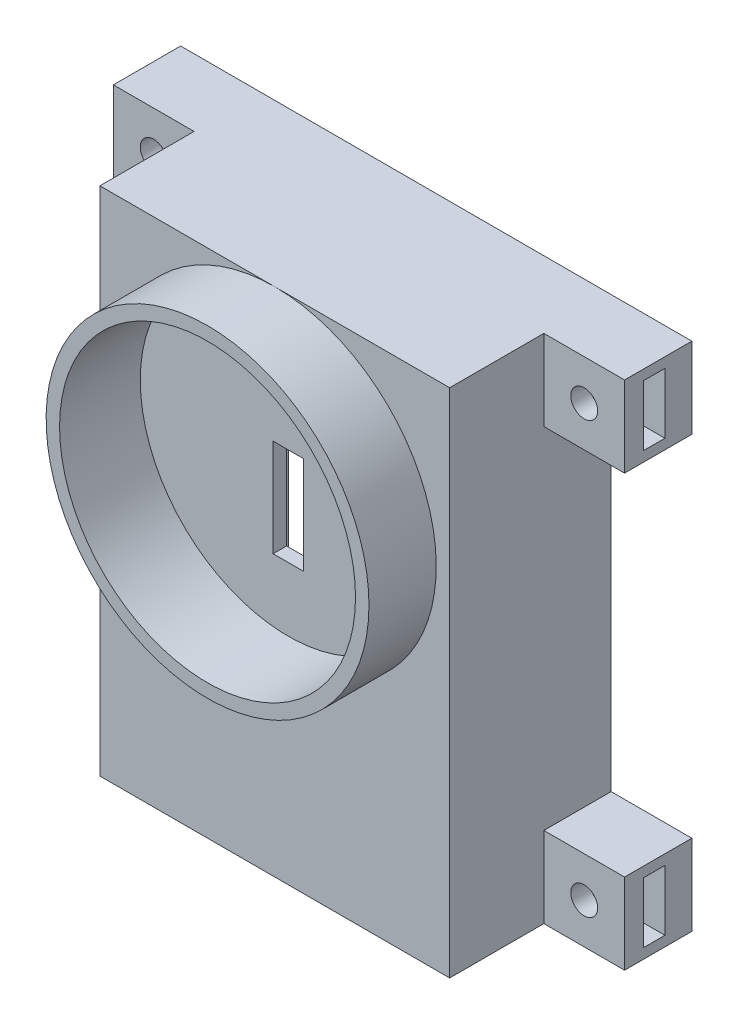
SolidWorks part; units mm, degrees
ref_plane "正面" through (0, 0, 0) normal (0, 0, 1) x (1, 0, 0)
ref_plane "平面" through (0, 0, 0) normal (0, 1, 0) x (1, 0, 0)
ref_plane "右側面" through (0, 0, 0) normal (1, 0, 0) x (0, 0, -1)
sketch "ｽｹｯﾁ1" plane through (0, 0, 0) normal (0, 0, 1) x (1, 0, 0)
  line L1 (13, -19) -> (-13, -19)
  line L2 (13, -19) -> (13, 19)
  line L3 (13, 19) -> (-13, 19)
  line L4 (-13, -19) -> (-13, 19)
  line L5 (13, -19) -> (-13, 19) construction
  line L6 (13, 19) -> (-13, -19) construction
  point P0 (0, 0)
  dimension "D1" = 38
  dimension "D2" = 26
extrude "ﾎﾞｽ - 押し出し1" add sketch "ｽｹｯﾁ1" along normal blind 12
sketch "ｽｹｯﾁ2" plane through (0, 0, 0) normal (0, 0, 1) x (1, 0, 0)
  line L1 (11, -17) -> (-11, -17)
  line L2 (11, -17) -> (11, 17)
  line L3 (11, 17) -> (-11, 17)
  line L4 (-11, -17) -> (-11, 17)
  line L5 (11, -17) -> (-11, 17) construction
  line L6 (11, 17) -> (-11, -17) construction
  point P0 (0, 0)
  dimension "D1" = 22
  dimension "D2" = 34
extrude "ｶｯﾄ - 押し出し1" cut sketch "ｽｹｯﾁ2" along normal blind 10
sketch "ｽｹｯﾁ3" plane through (0, 0, 0) normal (0, 0, 1) x (1, 0, 0)
  line L0 (13, 19) -> (-13, 19) construction
  line L1 (-1.125, 0.75) -> (1.125, 0.75)
  line L2 (-1.125, 0.75) -> (-1.125, 8)
  line L3 (-1.125, 8) -> (1.125, 8)
  line L4 (1.125, 0.75) -> (1.125, 8)
  line L5 (-1.125, 0.75) -> (1.125, 8) construction
  line L6 (-1.125, 8) -> (1.125, 0.75) construction
  point P0 (0, 4.375)
  dimension "D1" = 7.25
  dimension "D2" = 2.25
  dimension "D3" = 11
extrude "ｶｯﾄ - 押し出し3" cut sketch "ｽｹｯﾁ3" along normal blind 12
sketch "ｽｹｯﾁ4" plane through (0, 0, 0) normal (0, 0, 1) x (1, 0, 0)
  line L0 (13, -19) -> (13, 19) construction
  line L1 (13, 19) -> (19, 19)
  line L2 (13, 19) -> (13, 13)
  line L3 (13, 13) -> (19, 13)
  line L4 (19, 19) -> (19, 13)
  line L5 (13, -19) -> (19, -19)
  line L6 (13, -19) -> (13, -13)
  line L7 (13, -13) -> (19, -13)
  line L8 (19, -19) -> (19, -13)
  line L9 (-13, -19) -> (13, -19) construction
  line L10 (-13, -19) -> (-19, -19)
  line L11 (-13, -19) -> (-13, -13)
  line L12 (-13, -13) -> (-19, -13)
  line L13 (-19, -19) -> (-19, -13)
  line L14 (-13, 19) -> (-19, 19)
  line L15 (-13, 19) -> (-13, 13)
  line L16 (-13, 13) -> (-19, 13)
  line L17 (-19, 19) -> (-19, 13)
  dimension "D1" = 6
  dimension "D2" = 6
  dimension "D3" = 6
  dimension "D4" = 6
  dimension "D5" = 6
  dimension "D6" = 6
  dimension "D7" = 6
  dimension "D8" = 6
  dimension "D9" = 6
extrude "ﾎﾞｽ - 押し出し2" add sketch "ｽｹｯﾁ4" along normal blind 5
sketch "ｽｹｯﾁ5" plane through (0, 0, 0) normal (0, 0, 1) x (1, 0, 0)
  line L0 (-13, 19) -> (-19, 19) construction
  line L1 (-19, 19) -> (-19, 13) construction
  line L2 (-13, -13) -> (-19, -13) construction
  line L3 (19, -19) -> (19, -13) construction
  line L5 (13, 13) -> (19, 13) construction
  line L7 (19, -13) -> (13, -13) construction
  circle A0 centre (-16, 16) radius 1
  circle A1 centre (-16, -16) radius 1
  circle A2 centre (16, -16) radius 1
  circle A3 centre (16, 16) radius 1
  point P16 (16, 13)
  dimension "D1" = 3
  dimension "D2" = 3
  dimension "D3" = 3
  dimension "D4" = 2
  dimension "D5" = 2
  dimension "D6" = 3
  dimension "D7" = 2
  dimension "D8" = 2
  dimension "D9" = 3
  dimension "D10" = 3
extrude "ｶｯﾄ - 押し出し4" cut sketch "ｽｹｯﾁ5" along normal through all
sketch "ｽｹｯﾁ6" plane through (0, 0, 0) normal (0, 0, 1) x (1, 0, 0)
  line L0 (-19, 19) -> (-19, 13) construction
  line L1 (-17.1841, 17.9827) -> (-18.3091, 15.9659)
  line L2 (-18.3091, 15.9659) -> (-17.125, 13.9832)
  line L3 (-17.125, 13.9832) -> (-14.8159, 14.0173)
  line L4 (-14.8159, 14.0173) -> (-13.6909, 16.0341)
  line L5 (-13.6909, 16.0341) -> (-14.875, 18.0168)
  line L6 (-14.875, 18.0168) -> (-17.1841, 17.9827)
  line L7 (-19, -19) -> (-13, -19) construction
  line L8 (-17.0756, -13.9564) -> (-18.3076, -15.9097)
  line L9 (-18.3076, -15.9097) -> (-17.232, -17.9533)
  line L10 (-17.232, -17.9533) -> (-14.9244, -18.0436)
  line L11 (-14.9244, -18.0436) -> (-13.6924, -16.0903)
  line L12 (-13.6924, -16.0903) -> (-14.768, -14.0467)
  line L13 (-14.768, -14.0467) -> (-17.0756, -13.9564)
  line L14 (-13, 19) -> (-19, 19) construction
  line L15 (19, 19) -> (13, 19) construction
  line L16 (14.9393, 18.0514) -> (13.6931, 16.1072)
  line L17 (13.6931, 16.1072) -> (14.7537, 14.0557)
  line L18 (14.7537, 14.0557) -> (17.0607, 13.9486)
  line L19 (17.0607, 13.9486) -> (18.3069, 15.8928)
  line L20 (18.3069, 15.8928) -> (17.2463, 17.9443)
  line L21 (17.2463, 17.9443) -> (14.9393, 18.0514)
  line L22 (19, 13) -> (19, 19) construction
  line L23 (19, -19) -> (19, -13) construction
  line L24 (14.8545, -13.9947) -> (13.6906, -15.9894)
  line L25 (13.6906, -15.9894) -> (14.8362, -17.9947)
  line L26 (14.8362, -17.9947) -> (17.1455, -18.0053)
  line L27 (17.1455, -18.0053) -> (18.3094, -16.0106)
  line L28 (18.3094, -16.0106) -> (17.1638, -14.0053)
  line L29 (17.1638, -14.0053) -> (14.8545, -13.9947)
  line L30 (19, -13) -> (13, -13) construction
  line L31 (-19, -13) -> (-19, -19) construction
  circle A0 centre (-16, 16) radius 2 construction
  circle A1 centre (-16, -16) radius 2 construction
  circle A2 centre (16, 16) radius 2 construction
  circle A3 centre (16, -16) radius 2 construction
  point P23 (16, 19)
  point P45 (16, -13)
  dimension "D1" = 4
  dimension "D3" = 4
  dimension "D6" = 4
  dimension "D9" = 4
  dimension "D2" = 3
  dimension "D4" = 3
  dimension "D5" = 3
  dimension "D7" = 3
  dimension "D8" = 3
  dimension "D10" = 3
  dimension "D11" = 3
  dimension "D12" = 3
extrude "ｶｯﾄ - 押し出し5" cut sketch "ｽｹｯﾁ6" along normal blind 1.6 from offset 2
sketch "ｽｹｯﾁ7" plane through (0, 0, 12) normal (0, 0, 1) x (1, 0, 0)
  line L0 (-13, 19) -> (-13, -19) construction
  line L1 (13, 19) -> (-13, 19) construction
  line L2 (1.125, 8) -> (-1.125, 8) construction
  circle A0 centre (0, 7) radius 12
  circle A1 centre (0, 7) radius 11
  dimension "D1" = 24
  dimension "D4" = 22
  dimension "D2" = 13
  dimension "D3" = 12
  dimension "D5" = 1
extrude "ﾎﾞｽ - 押し出し3" add sketch "ｽｹｯﾁ7" along normal blind 5
sketch "ｽｹｯﾁ8" plane through (0, 0, 0) normal (1, 0, 0) x (0, 0, -1)
  line L0 (-17, 19) -> (-17, -5) construction
  circle A0 centre (-14, 5.2266) radius 1
  dimension "D1" = 2
  dimension "D2" = 3
extrude "ｶｯﾄ - 押し出し6" [suppressed] cut sketch "ｽｹｯﾁ8" against normal blind 20
pattern_linear "直線ﾊﾟﾀｰﾝ1" [suppressed] count 2 spacing 5
pattern_circular "円形ﾊﾟﾀｰﾝ1" [suppressed] count 12 over 360
sketch "ｽｹｯﾁ9" plane through (0, 0, 12) normal (0, 0, 1) x (1, 0, 0)
  circle A0 centre (0, 7) radius 11
  circle A1 centre (0, 7) radius 11 construction
  point P0 (0.0613, 4.3672)
  dimension "D3" = 22
extrude "ｶｯﾄ - 押し出し7" cut sketch "ｽｹｯﾁ9" against normal blind 1
sketch "ｽｹｯﾁ10" plane through (0, 0, 10) normal (0, 0, 1) x (1, 0, 0)
  line L1 (-7.2055, -13) -> (7.2055, -13)
  line L2 (-7.2055, -13) -> (-7.2055, -10)
  line L3 (-7.2055, -10) -> (7.2055, -10)
  line L4 (7.2055, -13) -> (7.2055, -10)
  line L5 (-7.2055, -13) -> (7.2055, -10) construction
  line L6 (-7.2055, -10) -> (7.2055, -13) construction
  point P0 (0, -11.5)
  dimension "D1" = 3
  dimension "D2" = 10
extrude "ﾎﾞｽ - 押し出し4" add sketch "ｽｹｯﾁ10" against normal blind 2
sketch "ｽｹｯﾁ11" plane through (0, 0, 0) normal (1, 0, 0) x (0, 0, -1)
  line L0 (0, 13) -> (0, 19) construction
  line L1 (-2, 13.75) -> (-3.6, 13.75)
  line L2 (-2, 13.75) -> (-2, 18.25)
  line L3 (-2, 18.25) -> (-3.6, 18.25)
  line L4 (-3.6, 13.75) -> (-3.6, 18.25)
  line L5 (-2, 13.75) -> (-3.6, 18.25) construction
  line L6 (-2, 18.25) -> (-3.6, 13.75) construction
  line L7 (-5, 19) -> (0, 19) construction
  line L8 (0, -19) -> (0, -13) construction
  line L9 (-2, -18.25) -> (-3.6, -18.25)
  line L10 (-2, -18.25) -> (-2, -13.75)
  line L11 (-2, -13.75) -> (-3.6, -13.75)
  line L12 (-3.6, -18.25) -> (-3.6, -13.75)
  line L13 (-2, -18.25) -> (-3.6, -13.75) construction
  line L14 (-2, -13.75) -> (-3.6, -18.25) construction
  line L15 (-5, -19) -> (0, -19) construction
  point P0 (-2.8, 16)
  point P9 (-2.8, -16)
  dimension "D1" = 1.6
  dimension "D2" = 4.5
  dimension "D3" = 2
  dimension "D4" = 0.75
  dimension "D5" = 4.5
  dimension "D6" = 1.6
  dimension "D7" = 2
  dimension "D8" = 0.75
extrude "ｶｯﾄ - 押し出し8" cut sketch "ｽｹｯﾁ11" against normal blind 4 from offset 20
sketch "ｽｹｯﾁ13" plane through (0, 0, 0) normal (1, 0, 0) x (0, 0, -1)
  line L0 (0, 13) -> (0, 19) construction
  line L1 (-2, 13.75) -> (-3.6, 13.75)
  line L2 (-2, 13.75) -> (-2, 18.25)
  line L3 (-2, 18.25) -> (-3.6, 18.25)
  line L4 (-3.6, 13.75) -> (-3.6, 18.25)
  line L5 (-2, 13.75) -> (-3.6, 18.25) construction
  line L6 (-2, 18.25) -> (-3.6, 13.75) construction
  line L7 (0, -19) -> (0, -13) construction
  line L9 (-2, -18.25) -> (-3.6, -18.25)
  line L10 (-2, -18.25) -> (-2, -13.75)
  line L11 (-2, -13.75) -> (-3.6, -13.75)
  line L12 (-3.6, -18.25) -> (-3.6, -13.75)
  line L13 (-2, -18.25) -> (-3.6, -13.75) construction
  line L14 (-2, -13.75) -> (-3.6, -18.25) construction
  point P0 (-2.8, 16)
  point P9 (-2.8, -16)
  dimension "D1" = 1.6
  dimension "D2" = 4.5
  dimension "D3" = 2
  dimension "D4" = 2
  dimension "D5" = 4.5
  dimension "D6" = 1.6
extrude "ｶｯﾄ - 押し出し9" cut sketch "ｽｹｯﾁ13" along normal blind 4 from offset 20
